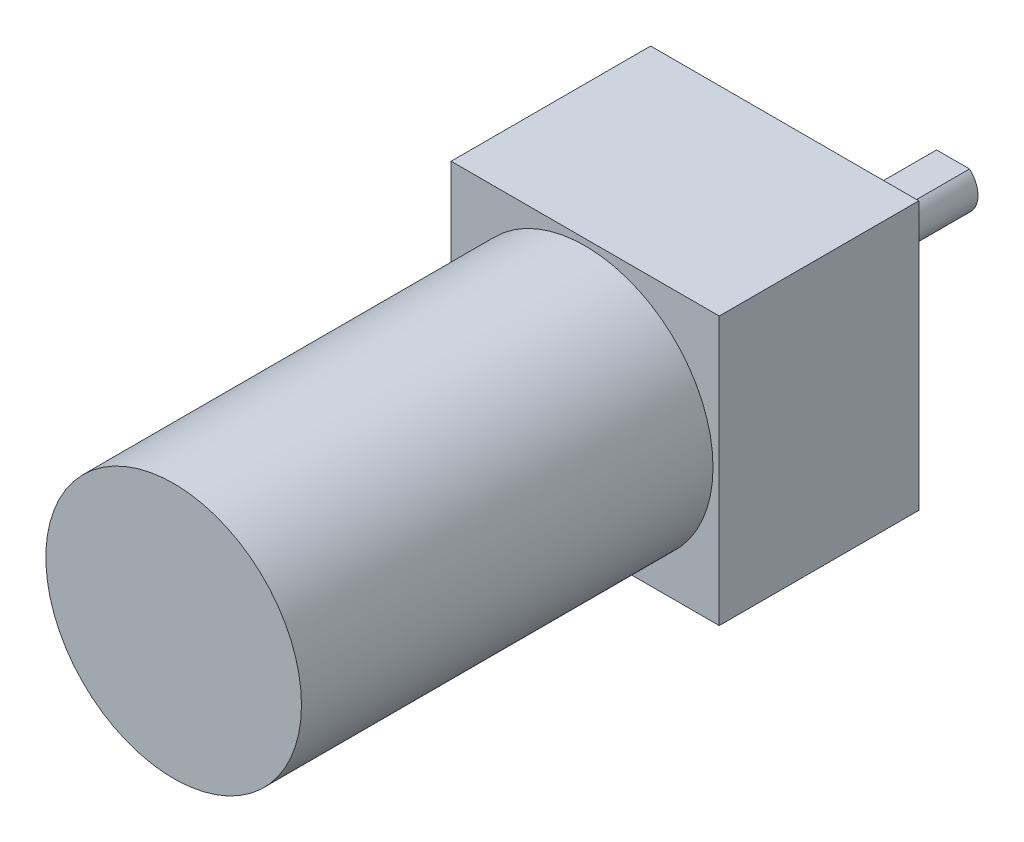
SolidWorks part; units mm, degrees
ref_plane "前视基准面" through (0, 0, 0) normal (0, 0, 1) x (1, 0, 0)
ref_plane "上视基准面" through (0, 0, 0) normal (0, 1, 0) x (1, 0, 0)
ref_plane "右视基准面" through (0, 0, 0) normal (1, 0, 0) x (0, 0, -1)
sketch "草图1" plane through (0, 0, 0) normal (0, 0, 1) x (1, 0, 0)
  line L0 (-27.4125, 0) -> (27.4125, 0) construction
  line L1 (-21.5, 21.5) -> (21.5, 21.5)
  line L2 (-21.5, 21.5) -> (-21.5, -21.5)
  line L3 (-21.5, -21.5) -> (21.5, -21.5)
  line L4 (21.5, 21.5) -> (21.5, -21.5)
  line L5 (0, 41.3875) -> (0, -41.3875) construction
  dimension "D1" = 43
  dimension "D2" = 43
extrude "凸台-拉伸1" add sketch "草图1" along normal blind 32
sketch "草图4" plane through (0, 0, 0) normal (1, 0, 0) x (0, 0, -1)
  line L0 (0, 0) -> (0, 7)
  line L1 (0, -21.5) -> (0, 21.5) construction
  line L2 (0, 7) -> (7, 7)
  line L3 (7, 7) -> (7, 4)
  line L4 (7, 4) -> (27, 4)
  line L5 (27, 4) -> (27, 0)
  line L6 (27, 0) -> (0, 0)
  dimension "D1" = 7
  dimension "D2" = 20
  dimension "D3" = 4
  dimension "D4" = 7
revolve "旋转1" add sketch "草图4" angle 360 about L6
sketch "草图5" plane through (0, 0, -27) normal (0, 0, -1) x (-1, 0, 0)
  line L0 (-4.9203, 3) -> (5.3805, 3)
  line L1 (5.3805, 3) -> (5.3805, 7.8602)
  line L2 (5.3805, 7.8602) -> (-4.9203, 7.8602)
  line L3 (-4.9203, 7.8602) -> (-4.9203, 3)
  dimension "D1" = 3
extrude "切除-拉伸1" cut sketch "草图5" against normal blind 18
sketch "草图6" plane through (0, 0, 32) normal (0, 0, 1) x (1, 0, 0)
  circle A0 centre (0, 0) radius 20.5
  dimension "D1" = 41
extrude "凸台-拉伸2" add sketch "草图6" along normal blind 66
sketch "草图7" plane through (0, 0, 0) normal (0, 0, -1) x (-1, 0, 0)
  line L0 (-23.4451, 0) -> (24.0368, 0) construction
  line L1 (0, 28.3265) -> (0, -26.1816) construction
  circle A0 centre (-18, 18) radius 2
  circle A4 centre (18, 18) radius 2
  circle A5 centre (18, -18) radius 2
  circle A6 centre (-18, -18) radius 2
  dimension "D1" = 18
  dimension "D2" = 18
  dimension "D3" = 4
extrude "切除-拉伸2" cut sketch "草图7" against normal blind 30
